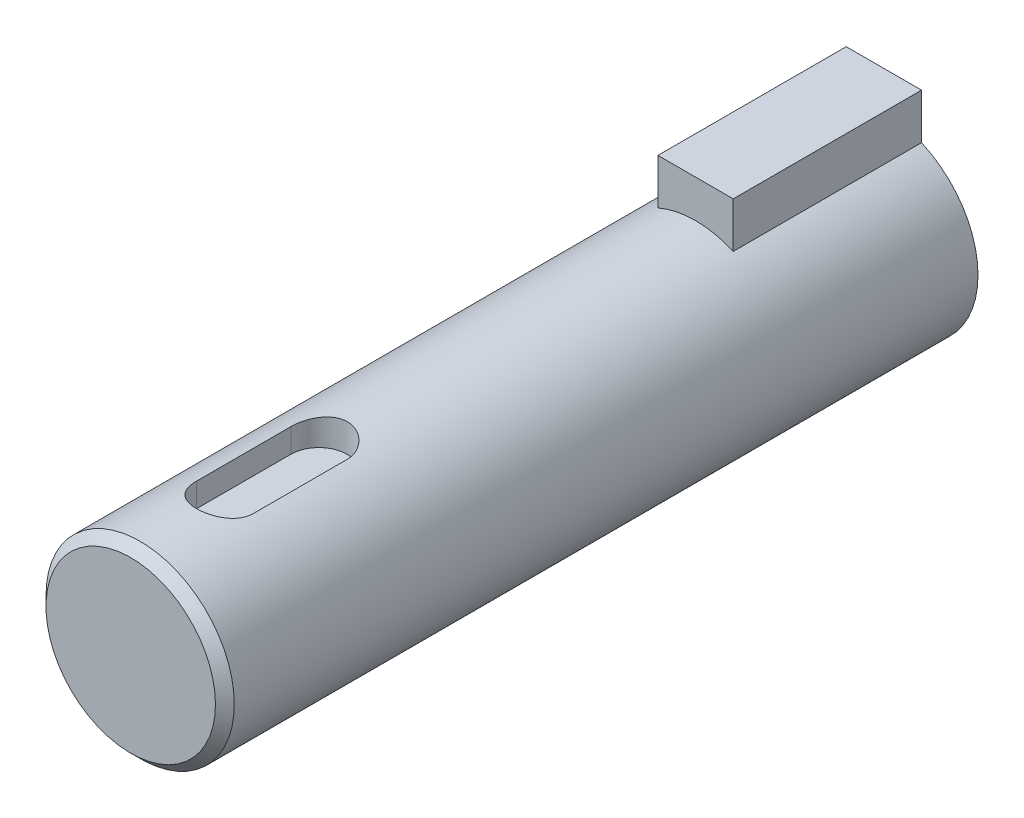
SolidWorks part; units mm, degrees
ref_plane "Front Plane" through (0, 0, 0) normal (0, 0, 1) x (1, 0, 0)
ref_plane "Top Plane" through (0, 0, 0) normal (0, 1, 0) x (1, 0, 0)
ref_plane "Right Plane" through (0, 0, 0) normal (1, 0, 0) x (0, 0, -1)
sketch "Sketch1" plane through (0, 0, 0) normal (0, 0, 1) x (1, 0, 0)
  line L0 (0, 0) -> (0, 10.1485) construction
  line L2 (-2, 7) -> (2, 7)
  line L3 (-2, 7) -> (-2, 4.5826)
  line L5 (2, 7) -> (2, 4.5826)
  arc A0 (-2, 4.5826) -> (2, 4.5826) centre (0, 0) ccw
  dimension "D1" = 10
  dimension "D2" = 4
  dimension "D3" = 7
extrude "Boss-Extrude1" add sketch "Sketch1" along normal blind 10
sketch "Sketch2" plane through (0, 0, 10) normal (0, 0, 1) x (1, 0, 0)
  circle A0 centre (0, 0) radius 5
extrude "Boss-Extrude2" add sketch "Sketch2" along normal blind 30
sketch "Sketch3" plane through (0, 0, 0) normal (0, 1, 0) x (1, 0, 0)
  line L0 (0, -40) -> (0, -14.5054) construction
  line L1 (-5, -40) -> (5, -40) construction
  line L2 (0, -35) -> (0, -30) construction
  line L3 (-1.5, -35) -> (-1.5, -30)
  line L4 (1.5, -35) -> (1.5, -30)
  arc A0 (-1.5, -35) -> (1.5, -35) centre (0, -35) ccw
  arc A1 (1.5, -30) -> (-1.5, -30) centre (0, -30) ccw
  point P7 (0, -32.5)
  point P12 (0, 0)
  point P13 (0, 0)
  dimension "D1" = 5
  dimension "D2" = 3
  dimension "D3" = 5
extrude "Cut-Extrude1" cut sketch "Sketch3" along normal through all from offset 3.5
chamfer "Chamfer1" distance 0.5 angle 45 1 edges at (5, 0, 40)
